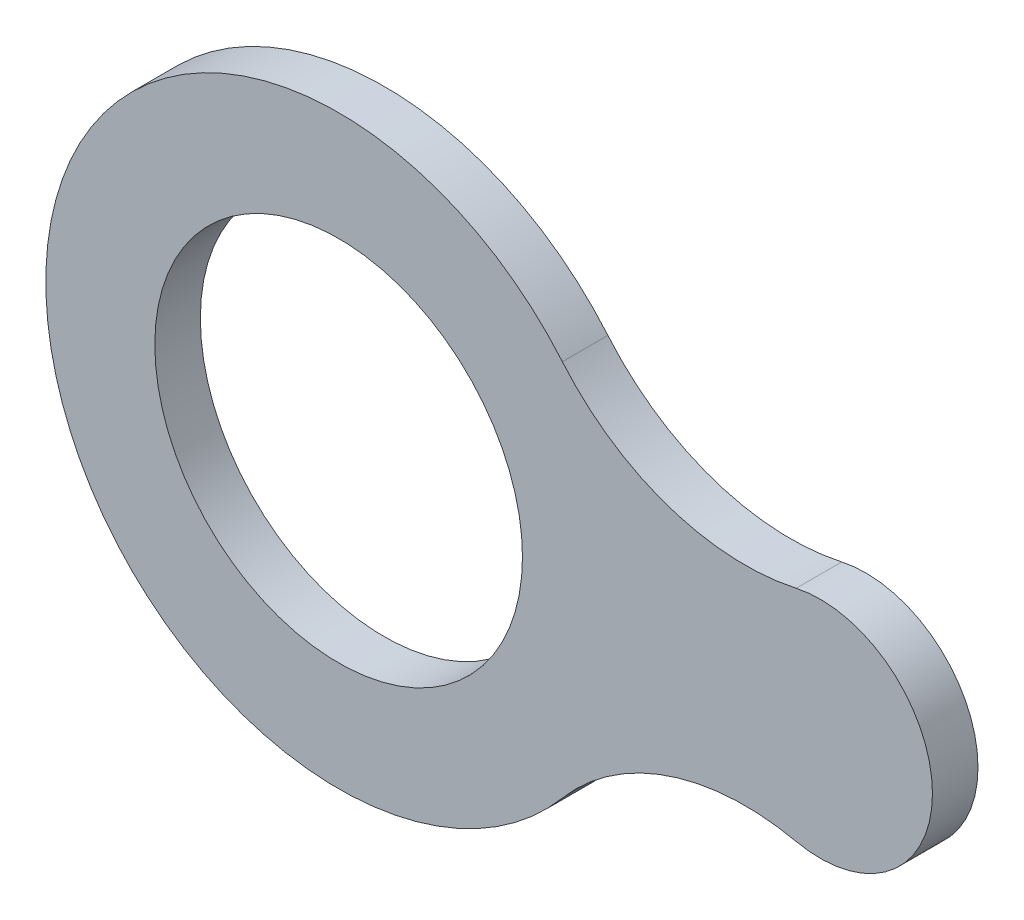
SolidWorks part; units mm, degrees
ref_plane "Front" through (0, 0, 0) normal (0, 0, 1) x (1, 0, 0)
ref_plane "Top" through (0, 0, 0) normal (0, 1, 0) x (1, 0, 0)
ref_plane "Right" through (0, 0, 0) normal (1, 0, 0) x (0, 0, -1)
sketch "Sketch1" plane through (0, 0, 0) normal (0, 0, 1) x (1, 0, 0)
  line L0 (-66.6645, 0) -> (123.8565, 0) construction
  circle A0 centre (0, 0) radius 28.25
  arc A1 (34.3799, 29.0348) -> (34.3799, -29.0348) centre (0, 0) ccw
  arc A2 (70.3096, 16.8506) -> (70.3096, -16.8506) centre (74, 0) cw
  arc A3 (34.3799, 29.0348) -> (70.3096, 16.8506) centre (62.4495, 52.7404) ccw
  arc A4 (34.3799, -29.0348) -> (70.3096, -16.8506) centre (62.4495, -52.7404) cw
  dimension "D1" = 32
  dimension "D3" = 56.5
  dimension "D4" = 45
  dimension "D5" = 17.25
  dimension "D6" = 119.5
extrude "Base-Extrude" add sketch "Sketch1" along normal blind 7
